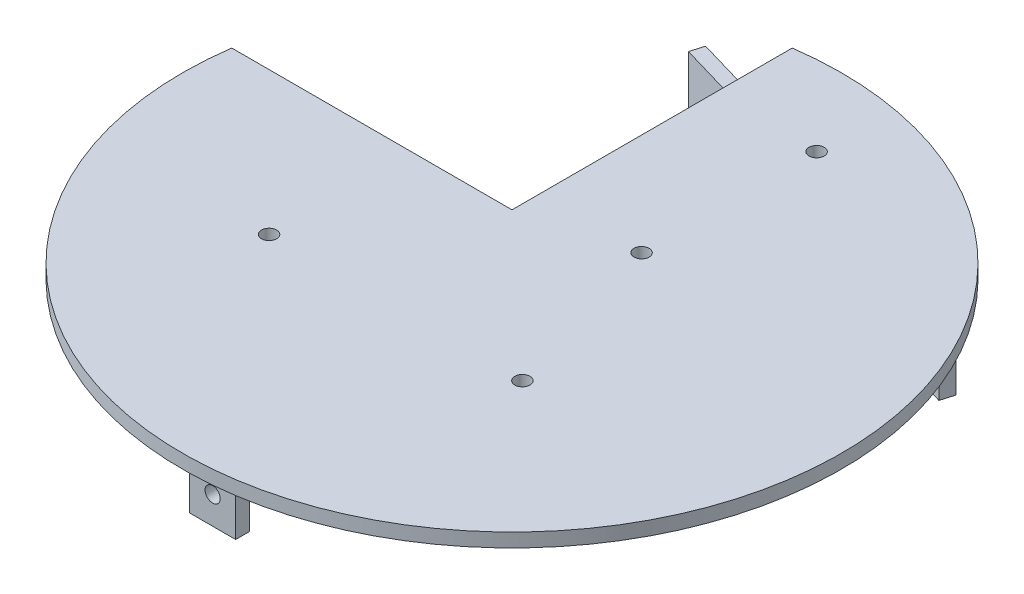
SolidWorks part; units mm, degrees
ref_plane "Front Plane" through (0, 0, 0) normal (0, 0, 1) x (1, 0, 0)
ref_plane "Top Plane" through (0, 0, 0) normal (0, 1, 0) x (1, 0, 0)
ref_plane "Right Plane" through (0, 0, 0) normal (1, 0, 0) x (0, 0, -1)
sketch "Sketch1" plane through (0, 0, 0) normal (0, 1, 0) x (1, 0, 0)
  line L3 (-10, 70.8427) -> (-10, 10)
  line L4 (-70.8427, 10) -> (-10, 10)
  arc A0 (-71.545, 0) -> (0, 71.545) centre (0, 0) ccw
  arc A1 (0, 71.545) -> (-10, 70.8427) centre (0, 0) ccw
  arc A2 (-71.545, 0) -> (-70.8427, 10) centre (0, 0) cw
  circle A3 centre (12.13, 16) radius 1.65
  circle A4 centre (12.13, 54) radius 1.65
  circle A5 centre (23.25, -21) radius 1.65
  circle A6 centre (-31.75, -21) radius 1.65
  dimension "D1" = 71.545
  dimension "D2" = 10
  dimension "D3" = 10
  dimension "D4" = 3.3
  dimension "D5" = 22.13
  dimension "D6" = 22.13
  dimension "D8" = 38
  dimension "D11" = 55
  dimension "D7" = 6
  dimension "D9" = 31
  dimension "D10" = 21.75
extrude "Boss-Extrude1" add sketch "Sketch1" along normal blind 3
sketch "Sketch2" plane through (0, 0, 0) normal (0, -1, 0) x (1, 0, 0)
  line L0 (0, 0) -> (0, 50000) construction
  line L1 (-23.6002, -61.9098) -> (53.1959, -39.4967)
  line L2 (-23.6002, -61.9098) -> (-22.7597, -64.7897)
  line L3 (-22.7597, -64.7897) -> (54.0364, -42.3765)
  line L4 (53.1959, -39.4967) -> (54.0364, -42.3765)
  line L5 (54.0364, -42.3765) -> (55.017, -45.7364) construction
  line L6 (-22.7597, -64.7897) -> (-21.7792, -68.1495) construction
  arc A0 (-10, -70.8427) -> (-70.8427, -10) centre (0, 0) ccw construction
  dimension "D1" = 73.73
  dimension "D2" = 3
  dimension "D3" = 80
  dimension "D4" = 3.5
extrude "Boss-Extrude2" add sketch "Sketch2" along normal blind 16 from surface at 0 starting at plane "Top Plane"
sketch "Sketch3" plane through (14.7979, 0, -50.7033) normal (-0.2802, 0, 0.96) x (0.96, 0, 0.2802)
  line L0 (-31, -8) -> (31, -8) construction
  line L1 (40, 0) -> (-25.8324, 0) construction
  line L2 (40, -16) -> (-40, -16) construction
  circle A0 centre (-31, -8) radius 1.65
  circle A1 centre (31, -8) radius 1.65
  point P8 (0, -16)
  point P9 (0, -8)
  dimension "D1" = 3.3
  dimension "D2" = 8
  dimension "D3" = 62
extrude "Cut-Extrude1" cut sketch "Sketch3" against normal blind 16
sketch "Sketch5" plane through (0, 0, 0) normal (0, -1, 0) x (-1, 0, 0)
  line L1 (5, -62) -> (-5, -62)
  line L2 (5, -62) -> (5, -65)
  line L3 (5, -65) -> (-5, -65)
  line L4 (-5, -62) -> (-5, -65)
  dimension "D1" = 3
extrude "Boss-Extrude3" add sketch "Sketch5" along normal blind 14
sketch "Sketch6" plane through (0, 0, 62) normal (0, 0, -1) x (-1, 0, 0)
  circle A0 centre (0, -7.9988) radius 1.65
extrude "Cut-Extrude2" cut sketch "Sketch6" against normal blind 14
